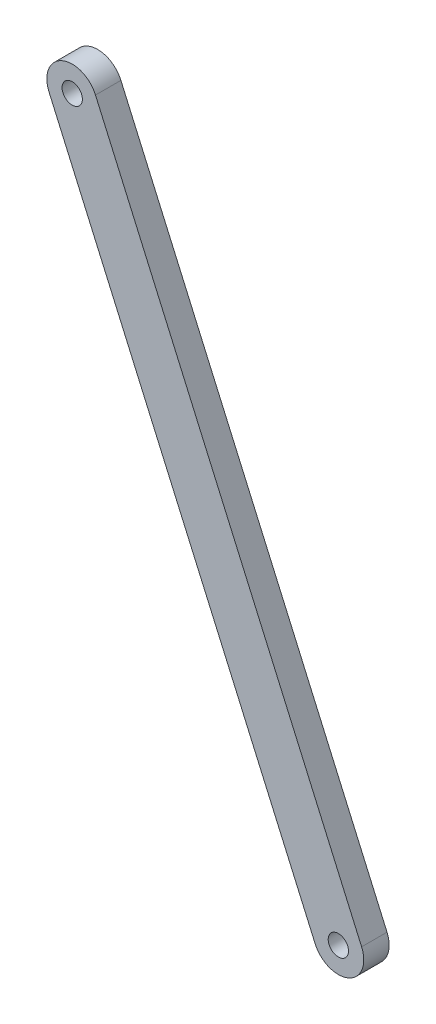
SolidWorks part; units mm, degrees
ref_plane "Front Plane" through (0, 0, 0) normal (0, 0, 1) x (1, 0, 0)
ref_plane "Top Plane" through (0, 0, 0) normal (0, 1, 0) x (1, 0, 0)
ref_plane "Right Plane" through (0, 0, 0) normal (1, 0, 0) x (0, 0, -1)
sketch "Sketch1" plane through (0, 0, 0) normal (0, 0, 1) x (1, 0, 0)
  line L0 (-74.8112, 158.2831) -> (-22.4423, 39.2978) construction
  line L3 (-31.595, 35.2694) -> (-83.9639, 154.2547) construction
  line L4 (-74.8112, 158.2831) -> (-22.4423, 39.2978)
  line L5 (-31.595, 35.2694) -> (-83.9639, 154.2547)
  circle A6 centre (-79.3875, 156.2689) radius 2 construction
  circle A7 centre (-27.0187, 37.2836) radius 2 construction
  arc A8 (-31.595, 35.2694) -> (-22.4423, 39.2978) centre (-27.0187, 37.2836) ccw construction
  arc A9 (-74.8112, 158.2831) -> (-83.9639, 154.2547) centre (-79.3875, 156.2689) ccw construction
  circle A10 centre (-79.3875, 156.2689) radius 2
  circle A11 centre (-27.0187, 37.2836) radius 2
  arc A12 (-31.595, 35.2694) -> (-22.4423, 39.2978) centre (-27.0187, 37.2836) ccw
  arc A13 (-74.8112, 158.2831) -> (-83.9639, 154.2547) centre (-79.3875, 156.2689) ccw
extrude "Boss-Extrude1" add sketch "Sketch1" against normal blind 5 from offset 5
